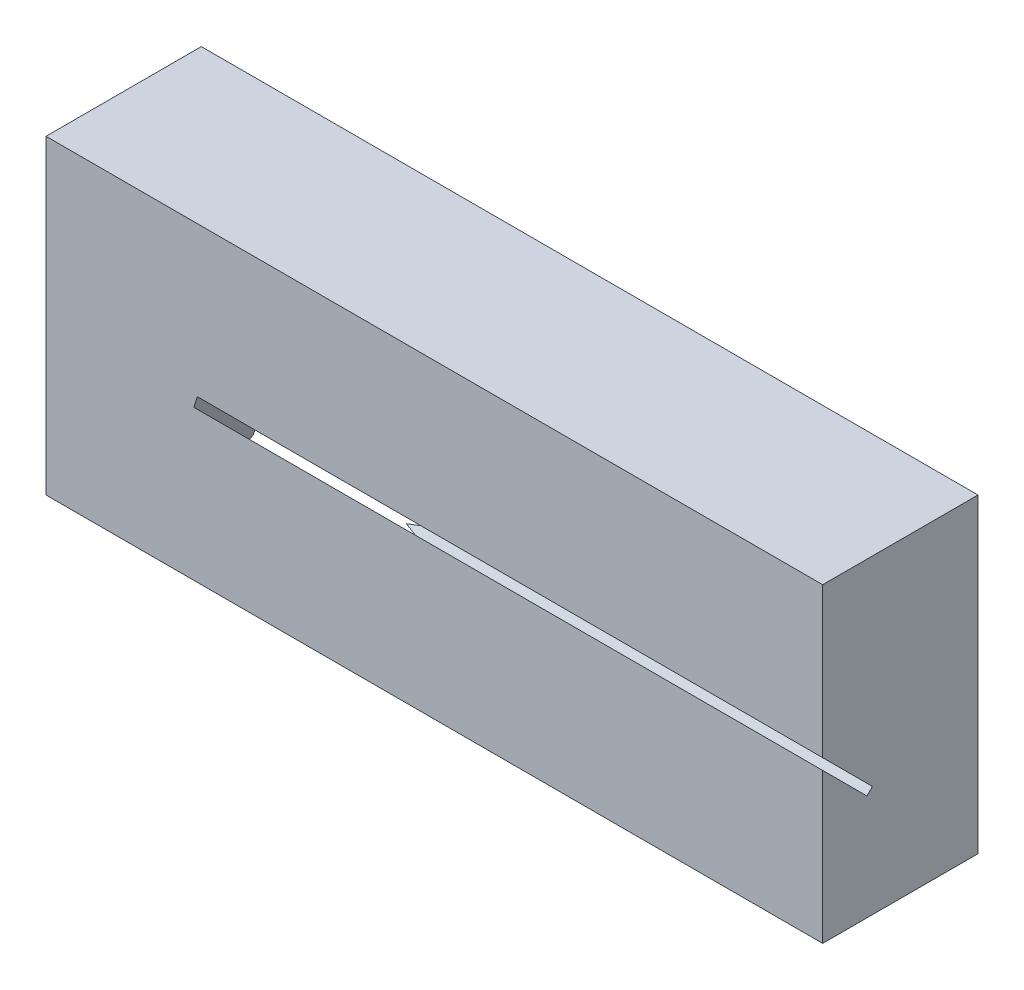
SolidWorks part; units mm, degrees
ref_plane "Front Plane" through (0, 0, 0) normal (0, 0, 1) x (1, 0, 0)
ref_plane "Top Plane" through (0, 0, 0) normal (0, 1, 0) x (1, 0, 0)
ref_plane "Right Plane" through (0, 0, 0) normal (1, 0, 0) x (0, 0, -1)
sketch "Sketch1" plane through (0, 0, 0) normal (0, 0, 1) x (1, 0, 0)
  line L1 (-25, 10) -> (25, 10)
  line L2 (-25, 10) -> (-25, -10)
  line L3 (-25, -10) -> (25, -10)
  line L4 (25, 10) -> (25, -10)
  line L5 (-25, 10) -> (25, -10) construction
  line L6 (-25, -10) -> (25, 10) construction
  point P1 (0, 0)
  dimension "D1" = 50
  dimension "D2" = 20
extrude "Boss-Extrude1" add sketch "Sketch1" along normal blind 10
ref_plane "Plane1" through (0, -5, 5) normal (0, -0.7071, 0.7071) x (1, 0, 0)
sketch "Sketch2" plane through (0, -5, 5) normal (0, -0.7071, 0.7071) x (1, 0, 0)
  line L0 (-23, -10.0711) -> (35.3756, 5.5706)
  line L1 (29.1639, 28.7528) -> (-10.4391, 18.1413)
  line L2 (-25, -7.0711) -> (25, -7.0711) construction
  line L3 (-23, -10.0711) -> (-10.4391, 18.1413)
  line L4 (-25, 0) -> (-25, -7.0711) construction
  line L5 (29.1639, 28.7528) -> (35.3756, 5.5706)
  line L6 (19.5046, 26.1646) -> (44.4889, 8.0125) construction
  line L7 (44.4889, 8.0125) -> (35.3756, 5.5706) construction
  point P1 (0, 0)
  point P4 (0, 0)
  dimension "D1" = 24
  dimension "D2" = 15
  dimension "D3" = 51
  dimension "D4" = 3
  dimension "D5" = 2
  dimension "D6" = 41
  dimension "D7" = 31
  dimension "D8" = 51
  dimension "D9" = 69.8696
extrude "Cut-Extrude1" cut sketch "Sketch2" against normal mid plane 0.5
